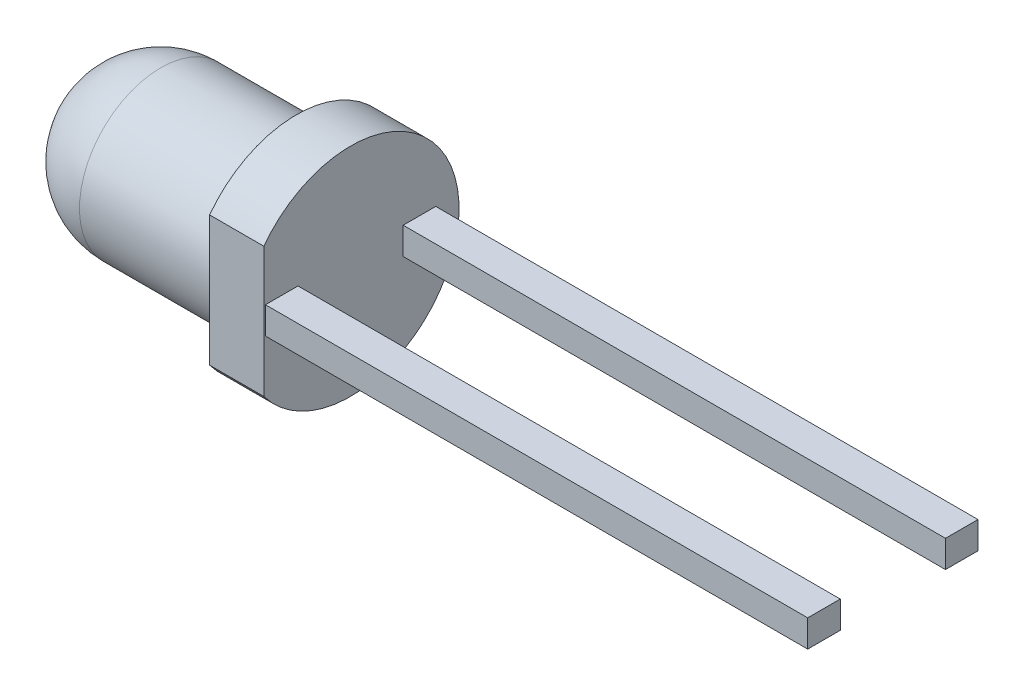
SolidWorks part; units mm, degrees
ref_plane "Спереди" through (0, 0, 0) normal (0, 0, 1) x (1, 0, 0)
ref_plane "Сверху" through (0, 0, 0) normal (0, 1, 0) x (1, 0, 0)
ref_plane "Справа" through (0, 0, 0) normal (1, 0, 0) x (0, 0, -1)
sketch "Эскиз1" plane through (0, 0, 0) normal (0, 0, 1) x (1, 0, 0)
  line L0 (0, 0) -> (-50000, 0) construction
  line L1 (0, 0) -> (0, 2)
  line L2 (0, 2) -> (-1, 2)
  line L3 (-1, 2) -> (-1, 1.5)
  line L4 (-1, 1.5) -> (-3.5, 1.5)
  line L5 (-5, 0) -> (0, 0)
  arc A0 (-3.5, 1.5) -> (-5, 0) centre (-3.5, 0) ccw
  dimension "D1" = 3
  dimension "D2" = 5
  dimension "D3" = 4
  dimension "D4" = 1
revolve "Повернуть1" add sketch "Эскиз1" angle 360 about L0
sketch "Эскиз2" plane through (0, 0, 0) normal (1, 0, 0) x (0, 0, -1)
  line L0 (0, 0) -> (50000, 0) construction
  line L1 (0, 0) -> (0, -50000) construction
  line L2 (-1.57, 0.25) -> (-0.97, 0.25)
  line L3 (-1.57, 0.25) -> (-1.57, -0.25)
  line L4 (-1.57, -0.25) -> (-0.97, -0.25)
  line L5 (-0.97, 0.25) -> (-0.97, -0.25)
  line L6 (-1.57, 0.25) -> (-0.97, -0.25) construction
  line L7 (-1.57, -0.25) -> (-0.97, 0.25) construction
  line L8 (0.97, 0.25) -> (1.57, 0.25)
  line L9 (0.97, 0.25) -> (0.97, -0.25)
  line L10 (0.97, -0.25) -> (1.57, -0.25)
  line L11 (1.57, 0.25) -> (1.57, -0.25)
  line L12 (0.97, 0.25) -> (1.57, -0.25) construction
  line L13 (0.97, -0.25) -> (1.57, 0.25) construction
  point P3 (-1.27, 0)
  point P8 (1.27, 0)
  point P15 (0, 0)
  dimension "D1" = 0.5
  dimension "D2" = 0.6
  dimension "D3" = 2.54
extrude "Бобышка-Вытянуть1" add sketch "Эскиз2" along normal blind 10 separate body
sketch "Эскиз3" plane through (-1, 0, 0) normal (-1, 0, 0) x (0, 0, 1)
  line L1 (2.4, 1.2) -> (1.6, 1.2)
  line L2 (2.4, 1.2) -> (2.4, -1.2)
  line L3 (2.4, -1.2) -> (1.6, -1.2)
  line L4 (1.6, 1.2) -> (1.6, -1.2)
  line L5 (2.4, 1.2) -> (1.6, -1.2) construction
  line L6 (2.4, -1.2) -> (1.6, 1.2) construction
  circle A0 centre (0, 0) radius 2 construction
  point P0 (2, 0)
  dimension "D1" = 0.4
extrude "Вырез-Вытянуть1" cut sketch "Эскиз3" against normal through all
